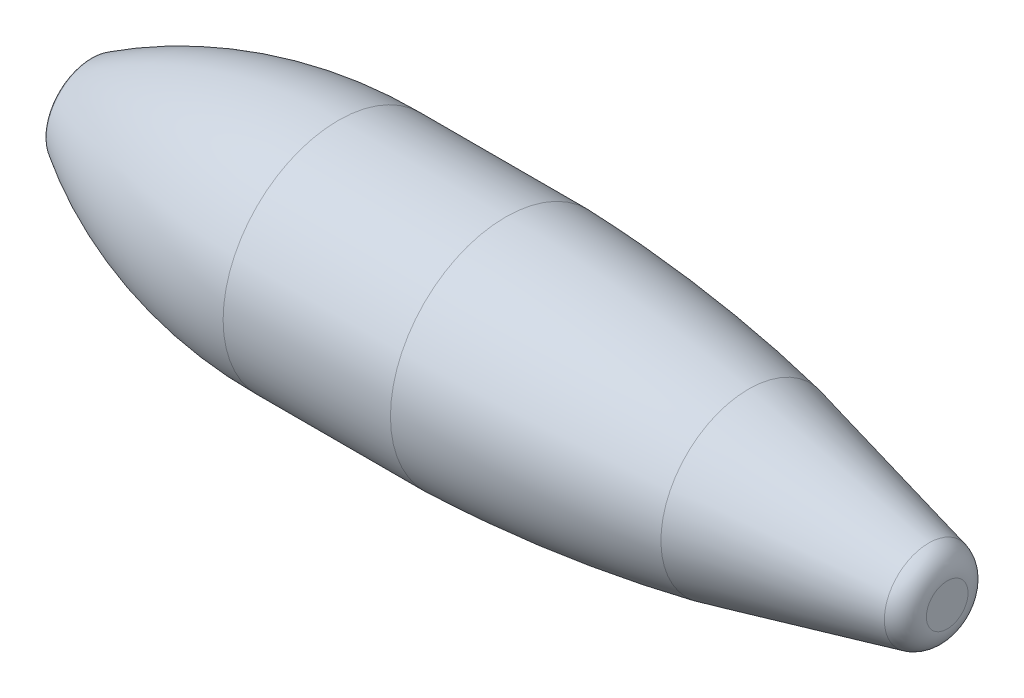
SolidWorks part; units mm, degrees
material "TNT explsoive"
ref_plane "Front Plane" through (0, 0, 0) normal (0, 0, 1) x (1, 0, 0)
ref_plane "Top Plane" through (0, 0, 0) normal (0, 1, 0) x (1, 0, 0)
ref_plane "Right Plane" through (0, 0, 0) normal (1, 0, 0) x (0, 0, -1)
sketch "Sketch1" plane through (0, 0, 0) normal (0, 0, 1) x (1, 0, 0)
  line L0 (-198.645, 0) -> (198.645, 0) construction
  line L1 (-182.645, 14.5) -> (-182.645, 0)
  line L2 (-198.645, 0) -> (-158.065, 0) construction
  line L3 (-158.065, 0) -> (-158.065, 42.12) construction
  line L4 (171.905, 0) -> (-182.645, 0)
  line L5 (-158.065, 0) -> (-82.295, 0) construction
  line L26 (89.705, 0) -> (89.705, 44.67) construction
  line L34 (89.705, 0) -> (89.705, 36.22) construction
  line L35 (171.905, 0) -> (171.905, 8.6153)
  line L36 (-10.775, 0) -> (-10.775, 47.63) construction
  line L37 (-10.775, 47.63) -> (-79.995, 47.63)
  line L40 (-182.645, 14.5) -> (-182.645, 17.3451)
  line L41 (164.2378, 18.3394) -> (89.705, 36.22)
  arc A3 (-10.775, 47.63) -> (89.705, 36.22) centre (-30.7217, -576.1612) cw
  arc A4 (-181.5978, 19.2189) -> (-79.995, 47.63) centre (-81.1844, -143.9963) cw
  arc A5 (-181.5978, 19.2189) -> (-182.645, 17.3451) centre (-180.445, 17.3451) ccw
  arc A6 (164.2378, 18.3394) -> (171.905, 8.6153) centre (161.905, 8.6153) cw
  dimension "D27" = 624.11
  dimension "D32" = 191.63
  dimension "D33" = 4.4
  dimension "D34" = 10
  dimension "D1" = 397.29
  dimension "D2" = 40.58
  dimension "D4" = 42.12
  dimension "D5" = 75.77
  dimension "D17" = 44.67
  dimension "D24" = 36.22
  dimension "D25" = 47.63
  dimension "D26" = 100.48
  dimension "D30" = 19.2189
  dimension "D36" = 74.5328
revolve "Revolve1" add sketch "Sketch1" angle 360 about L4
